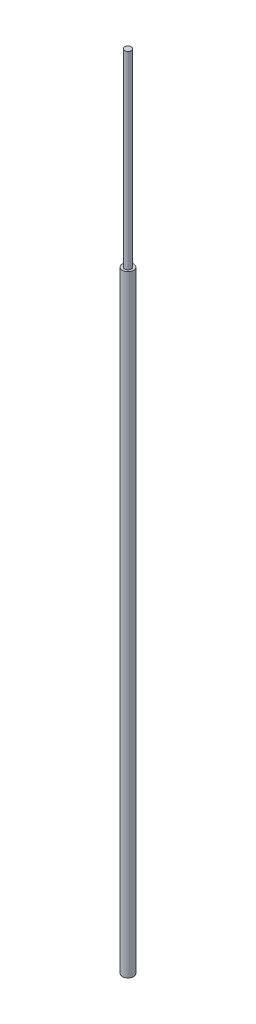
SolidWorks part; units mm, degrees
ref_plane "Front" through (0, 0, 0) normal (0, 0, 1) x (1, 0, 0)
ref_plane "Top" through (0, 0, 0) normal (0, 1, 0) x (1, 0, 0)
ref_plane "Right" through (0, 0, 0) normal (1, 0, 0) x (0, 0, -1)
sketch "Sketch1" plane through (0, 0, 0) normal (0, 1, 0) x (1, 0, 0)
  circle A0 centre (0, 0) radius 12.7
  dimension "D1" = 25.4
extrude "Boss-Extrude1" add sketch "Sketch1" along normal blind 1397
sketch "Sketch2" plane through (0, 1397, 0) normal (0, 1, 0) x (1, 0, 0)
  circle A0 centre (0, 0) radius 7.637
extrude "Boss-Extrude2" add sketch "Sketch2" along normal blind 431.8
